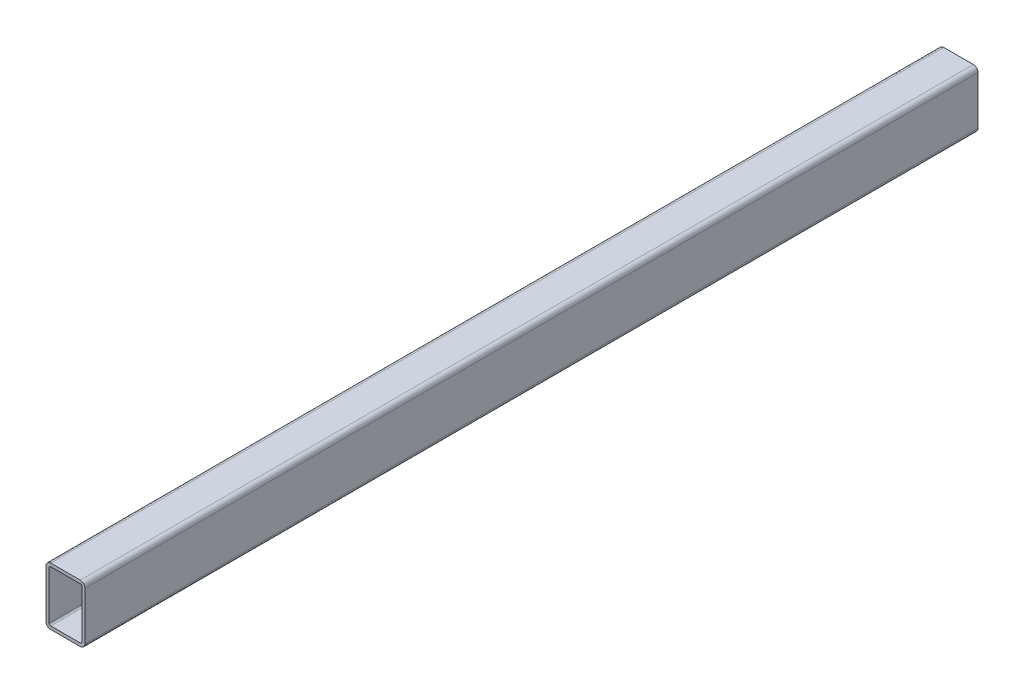
SolidWorks part; units mm, degrees
material "Alloy Steel"
ref_plane "Front" through (0, 0, 0) normal (0, 0, 1) x (1, 0, 0)
ref_plane "Top" through (0, 0, 0) normal (0, 1, 0) x (1, 0, 0)
ref_plane "Right" through (0, 0, 0) normal (1, 0, 0) x (0, 0, -1)
sketch "Sketch1" plane through (0, 0, 0) normal (0, 0, 1) x (1, 0, 0)
  line L0 (0, 40.8909) -> (0, -24.1212) construction
  line L1 (-9.5, 37) -> (9.5, 37)
  line L2 (-12.5, 34) -> (-12.5, 3)
  line L3 (-9.5, 0) -> (9.5, 0)
  line L4 (12.5, 34) -> (12.5, 3)
  arc A0 (-12.5, 3) -> (-9.5, 0) centre (-9.5, 3) ccw
  arc A1 (9.5, 0) -> (12.5, 3) centre (9.5, 3) ccw
  arc A2 (9.5, 37) -> (12.5, 34) centre (9.5, 34) cw
  arc A3 (-9.5, 37) -> (-12.5, 34) centre (-9.5, 34) ccw
  point P9 (-12.5, 0)
  point P12 (12.5, 0)
  point P15 (12.5, 37)
  dimension "D3" = 3
  dimension "D1" = 37
  dimension "D2" = 25
extrude "Extrude-Thin1" add sketch "Sketch1" along normal mid plane 574 thin contours L1 A2 L4 A1 L3 A0 L2 A3
